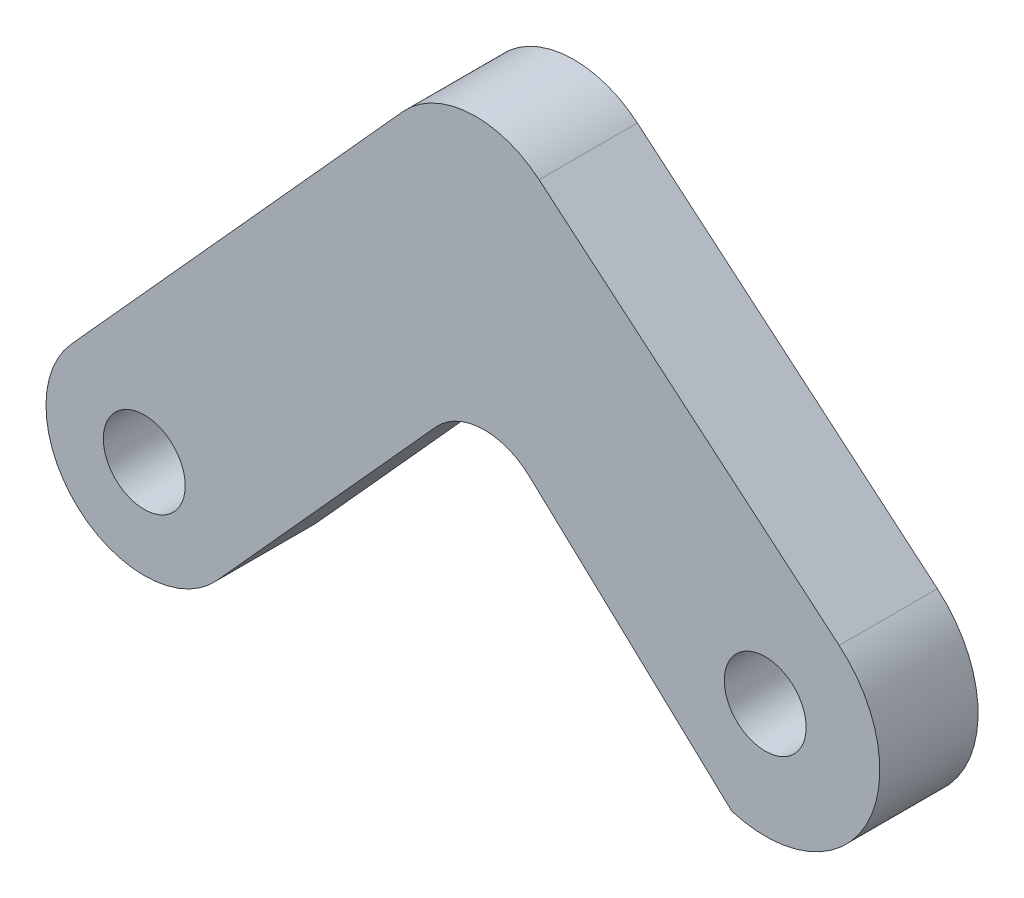
SolidWorks part; units mm, degrees
ref_plane "Front Plane" through (0, 0, 0) normal (0, 0, 1) x (1, 0, 0)
ref_plane "Top Plane" through (0, 0, 0) normal (0, 1, 0) x (1, 0, 0)
ref_plane "Right Plane" through (0, 0, 0) normal (1, 0, 0) x (0, 0, -1)
sketch "Sketch1" plane through (0, 0, 0) normal (0, 0, 1) x (1, 0, 0)
  line L0 (0, 0) -> (84.7921, -76.5803) construction
  line L1 (0, 0) -> (-52.652, -58.2979) construction
  line L3 (-0.2156, 4.2372) -> (-12.2802, -9.1212)
  line L5 (0.2156, -4.2372) -> (-7.8275, -13.1427)
  line L6 (-0.2156, 4.2372) -> (11.1633, -5.3686)
  line L7 (0.2156, -4.2372) -> (-50.4256, -60.3087) construction
  line L8 (-0.2156, 4.2372) -> (-54.8784, -56.2872) construction
  line L9 (0.2156, -4.2372) -> (82.7813, -78.8067) construction
  line L10 (-0.2156, 4.2372) -> (86.8029, -74.3539) construction
  line L11 (0.2156, -4.2372) -> (7.8857, -11.3912)
  arc A0 (-12.2802, -9.1212) -> (-7.8275, -13.1427) centre (-10.0538, -11.1319) ccw
  circle A2 centre (-10.0538, -11.1319) radius 1.25
  arc A4 (7.8857, -11.3912) -> (11.1633, -5.3686) centre (8.9056, -8.0431) ccw
  circle A5 centre (8.9056, -8.0431) radius 1.25
  dimension "D5" = 2.5
  dimension "D8" = 2.5
  dimension "D9" = 7
  dimension "D3" = 15
  dimension "D4" = 12
  dimension "D7" = 90
  dimension "D1" = 3
  dimension "D2" = 3
extrude "Boss-Extrude1" add sketch "Sketch1" along normal blind 3
fillet "Fillet1" radius 3 1 edges at (-0.2156, 4.2372, 1.5)
fillet "Fillet2" radius 2 1 edges at (0.2156, -4.2372, 1.5)
